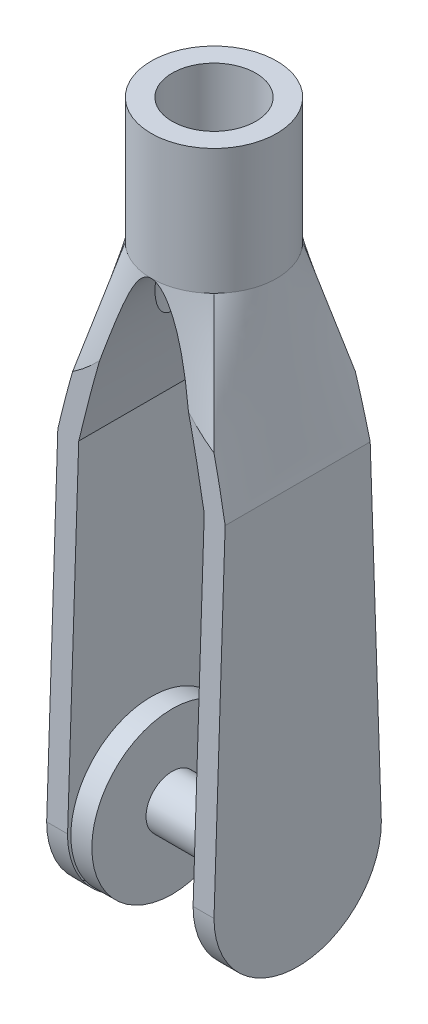
SolidWorks part; units mm, degrees
ref_plane "Front Plane" through (0, 0, 0) normal (0, 0, 1) x (1, 0, 0)
ref_plane "Top Plane" through (0, 0, 0) normal (0, 1, 0) x (1, 0, 0)
ref_plane "Right Plane" through (0, 0, 0) normal (1, 0, 0) x (0, 0, -1)
sketch "Sketch6" plane through (0, 0, 0) normal (0, 1, 0) x (1, 0, 0)
  line L1 (-2, -2) -> (2, -2)
  line L2 (-2, -2) -> (-2, 2)
  line L3 (-2, 2) -> (2, 2)
  line L4 (2, -2) -> (2, 2)
  line L5 (-2, -2) -> (2, 2) construction
  line L6 (-2, 2) -> (2, -2) construction
  point P0 (0, 0)
  dimension "D1" = 4
ref_plane "Plane3" through (0, 4, 0) normal (0, 1, 0) x (1, 0, 0)
sketch "Sketch7" plane through (0, 4, 0) normal (0, 1, 0) x (1, 0, 0)
  circle A0 centre (0, 0) radius 1.5
  dimension "D1" = 3
loft "Loft1" add profiles "Sketch7", "Sketch6"
sketch "Sketch8" plane through (0, 4, 0) normal (0, 1, 0) x (1, 0, 0)
  circle A0 centre (0, 0) radius 1.5
  dimension "D1" = 3
extrude "Boss-Extrude4" add sketch "Sketch8" along normal blind 3
sketch "Sketch9" plane through (0, 0, 0) normal (0, -1, 0) x (1, 0, 0)
  line L1 (2, 2) -> (-2, 2)
  line L2 (2, 2) -> (2, -2)
  line L3 (2, -2) -> (-2, -2)
  line L4 (-2, 2) -> (-2, -2)
  line L5 (2, 2) -> (-2, -2) construction
  line L6 (2, -2) -> (-2, 2) construction
  point P0 (0, 0)
extrude "Boss-Extrude5" add sketch "Sketch9" along normal blind 10
sketch "Sketch10" plane through (0, 0, -2) normal (0, 0, -1) x (-1, 0, 0)
  line L0 (-1.5, -10) -> (-1.5, 0)
  line L1 (2, -10) -> (-2, -10) construction
  line L2 (1.5, 0) -> (1.5, -10)
  line L3 (1.5, -10) -> (-1.5, -10)
  line L5 (2, 0) -> (-2, 0) construction
  line L6 (1.5, 7) -> (-1.5, 7) construction
  conic Q0 (-1.5, 0) -> (1.5, 0) control (0, 7) rho 0.571429
  point P4 (0, -10)
  dimension "D1" = 10
  dimension "D2" = 3
  dimension "D3" = 4
extrude "Cut-Extrude1" cut sketch "Sketch10" against normal through all both and the other way through all
sketch "Sketch11" plane through (2, 0, 0) normal (1, 0, 0) x (0, 0, -1)
  line L0 (2, -10) -> (2, 0) construction
  line L1 (-2, -10) -> (-2, 0) construction
  line L2 (2, -8) -> (1.5, 7)
  line L3 (1.5, 7) -> (-1.5, 7)
  line L4 (-1.5, 7) -> (-2, -8)
  line L5 (2, -10) -> (-2, -10) construction
  arc A0 (2, -8) -> (-2, -8) centre (0, -8) cw
extrude "Cut-Extrude-Thin1" cut sketch "Sketch11" against normal blind 10 thin
sketch "Sketch12" plane through (2, 0, 0) normal (1, 0, 0) x (0, 0, -1)
  circle A0 centre (0, -8.0798) radius 0.625
  dimension "D1" = 1.25
extrude "Cut-Extrude2" cut sketch "Sketch12" against normal through all both and the other way through all
sketch "Sketch13" plane through (0, 7, 0) normal (0, 1, 0) x (1, 0, 0)
  circle A0 centre (0, 0) radius 1
  dimension "D1" = 2
extrude "Cut-Extrude3" cut sketch "Sketch13" against normal through all both and the other way through all
sketch "Sketch14" plane through (-1.5, 0, 0) normal (1, 0, 0) x (0, 0, -1)
  circle A0 centre (0, -8.0798) radius 1.9202
extrude "Boss-Extrude6" add sketch "Sketch14" along normal blind 0.5
sketch "Sketch15" plane through (-1, 0, 0) normal (1, 0, 0) x (0, 0, -1)
  circle A0 centre (0, -8.0798) radius 0.625
extrude "Boss-Extrude7" add sketch "Sketch15" along normal blind 3
